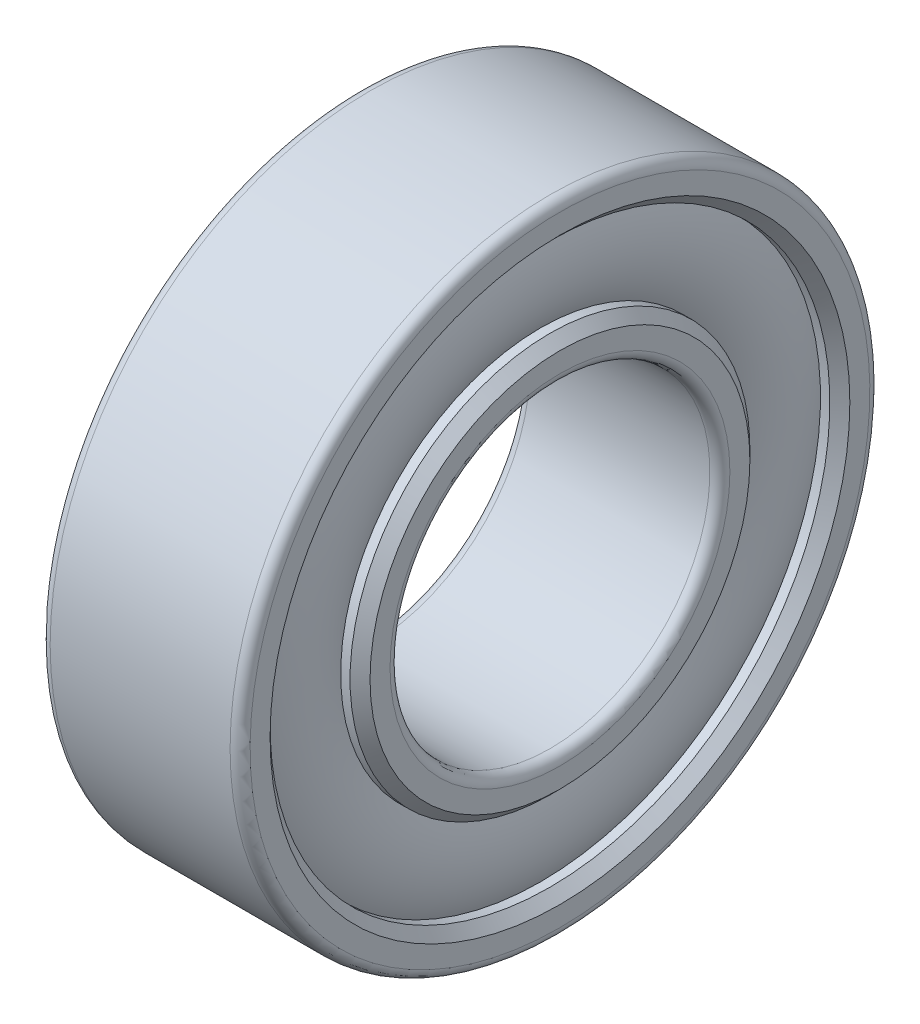
SolidWorks part; units mm, degrees
material "Chrome Stainless Steel"
ref_plane "Front Plane" through (0, 0, 0) normal (0, 0, 1) x (1, 0, 0)
ref_plane "Top Plane" through (0, 0, 0) normal (0, 1, 0) x (1, 0, 0)
ref_plane "Right Plane" through (0, 0, 0) normal (1, 0, 0) x (0, 0, -1)
sketch "Sketch1" plane through (0, 0, 0) normal (0, 0, 1) x (1, 0, 0)
  line L0 (0, 0) -> (5, 0) construction
  line L1 (0, -4.25) -> (0, -4.75)
  line L2 (5, -4.25) -> (5, -4.75)
  line L3 (0.25, -4) -> (4.75, -4)
  line L4 (0.25, -8) -> (4.75, -8)
  line L5 (0, -6) -> (5, -6) construction
  line L6 (2.5, -6) -> (2.5, -8) construction
  line L7 (0.25, -5) -> (0.4844, -5)
  line L8 (0.25, -7) -> (0.4844, -7)
  line L9 (0, -7.25) -> (0, -7.75)
  line L10 (4.75, -5) -> (4.5156, -5)
  line L11 (4.75, -7) -> (4.5156, -7)
  line L12 (5, -7.25) -> (5, -7.75)
  line L13 (0, -4.75) -> (0.25, -5)
  line L14 (0, -7.25) -> (0.25, -7)
  line L15 (5, -7.25) -> (4.75, -7)
  line L16 (5, -4.75) -> (4.75, -5)
  line L17 (2.5, -6) -> (2.5, -4) construction
  line L18 (4.75, -5) -> (4.75, -7) construction
  line L19 (5, -4.75) -> (5, -5) construction
  line L20 (5, -5) -> (4.75, -5) construction
  line L21 (5, -7.25) -> (5, -7) construction
  line L22 (5, -7) -> (4.75, -7) construction
  line L23 (0.25, -7) -> (0, -7) construction
  line L24 (0, -7) -> (0, -7.25) construction
  arc A0 (0.4844, -5) -> (0.4844, -7) centre (2.5, -6) ccw
  arc A1 (0.25, -8) -> (0, -7.75) centre (0.25, -7.75) cw
  arc A2 (5, -7.75) -> (4.75, -8) centre (4.75, -7.75) cw
  arc A3 (4.75, -4) -> (5, -4.25) centre (4.75, -4.25) cw
  arc A4 (0.25, -4) -> (0, -4.25) centre (0.25, -4.25) ccw
  arc A5 (4.5156, -7) -> (4.5156, -5) centre (2.5, -6) ccw
  point P11 (0, -11.75)
  point P12 (9, -11.75)
  point P13 (0, -13.75)
  point P14 (9, -13.75)
  point P15 (0, -9.75)
  point P16 (9, -9.75)
  point P19 (0, -5)
  point P20 (0, -7)
  point P23 (5, -5)
  point P25 (5, -7)
  dimension "D6" = 0.25
  dimension "D1" = 4
  dimension "D2" = 8
  dimension "D3" = 5
  dimension "D5" = 1
revolve "Revolve1" add sketch "Sketch1" angle 360 about L0
